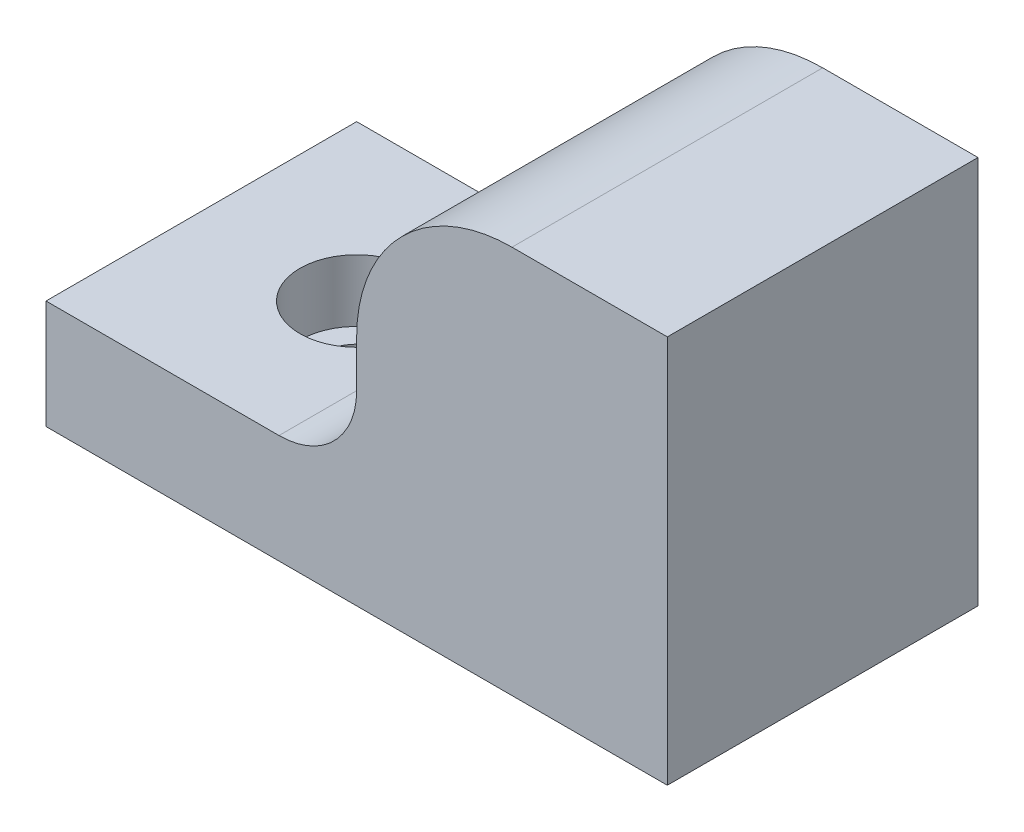
SolidWorks part; units mm, degrees
ref_plane "前基準面" through (0, 0, 0) normal (0, 0, 1) x (1, 0, 0)
ref_plane "上基準面" through (0, 0, 0) normal (0, 1, 0) x (1, 0, 0)
ref_plane "右基準面" through (0, 0, 0) normal (1, 0, 0) x (0, 0, -1)
sketch "草圖1" plane through (0, 0, 0) normal (0, 0, 1) x (1, 0, 0)
  line L1 (20, 25) -> (0, 25)
  line L2 (20, 25) -> (20, 0)
  line L7 (20, 0) -> (0, 0)
  line L8 (0, 25) -> (0, 0)
  line L9 (-20, 7) -> (0, 7)
  line L10 (-20, 7) -> (-20, 0)
  line L11 (-20, 0) -> (0, 0)
  line L12 (0, 7) -> (0, 0)
  line L13 (-20, 7) -> (0, 0) construction
  line L14 (-20, 0) -> (0, 7) construction
  line L15 (20, 25) -> (0, 0) construction
  line L16 (20, 0) -> (0, 25) construction
  point P0 (-10, 3.5)
  point P4 (10, 12.5)
  dimension "D1" = 20
  dimension "D2" = 25
  dimension "D3" = 7
  dimension "D4" = 20
extrude "填料-伸長1" add sketch "草圖1" along normal mid plane 20
sketch "草圖2" plane through (0, 7, 0) normal (0, 1, 0) x (1, 0, 0)
  line L0 (-55, 0) -> (55, 0) construction
  line L1 (-20, -10) -> (-20, 10) construction
  circle A0 centre (-10, 0) radius 3.65
  dimension "D2" = 7.3
  dimension "D1" = 10
extrude "除料-伸長1" cut sketch "草圖2" against normal blind 4
sketch "草圖3" plane through (0, 3, 0) normal (0, 1, 0) x (1, 0, 0)
  circle A0 centre (-10, 0) radius 2.25
  dimension "D1" = 4.5
extrude "除料-伸長2" cut sketch "草圖3" against normal up to next
ref_plane "平面1" through (10, 0, 0) normal (1, 0, 0) x (0, 0, -1)
sketch "草圖4" plane through (0, 0, 0) normal (0, -1, 0) x (1, 0, 0)
  line L0 (13.75, 0) -> (-13.75, 0) construction
  line L2 (20, 10) -> (20, -10) construction
  circle A0 centre (10, 0) radius 3.4
  dimension "D1" = 6.8
  dimension "D2" = 10
sketch "草圖5" plane through (10, 0, 10) normal (1, 0, 0) x (0, 0, -1)
  line L0 (10, 0) -> (10, 12)
  line L1 (6.6, 0) -> (13.4, 0) construction
  line L2 (18, 20) -> (20, 20)
  line L3 (20, 25) -> (20, 0) construction
  line L4 (21, 0) -> (-1, 0) construction
  arc A0 (10, 12) -> (18, 20) centre (18, 12) cw
  dimension "D2" = 8
  dimension "D1" = 20
sweep "除料-掃出1" cut profiles "草圖4" path "草圖5"
fillet "圓角1" radius 5 1 edges at (0, 7, 0)
fillet "圓角2" radius 10 1 edges at (0, 25, 0)
